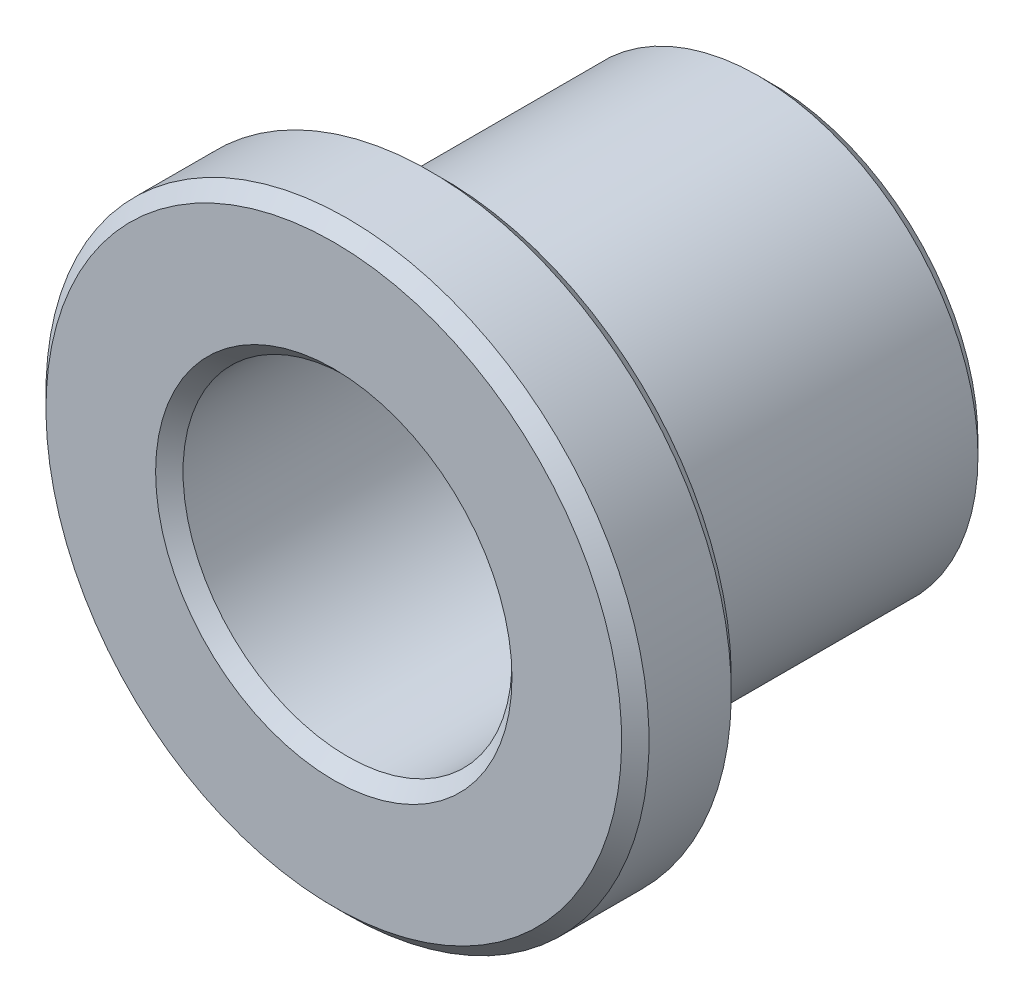
SolidWorks part; units mm, degrees
material "1.0114 (S235J0)"
ref_plane "Front Plane" through (0, 0, 0) normal (0, 0, 1) x (1, 0, 0)
ref_plane "Top Plane" through (0, 0, 0) normal (0, 1, 0) x (1, 0, 0)
ref_plane "Right Plane" through (0, 0, 0) normal (1, 0, 0) x (0, 0, -1)
sketch "Sketch1" plane through (0, 0, 0) normal (1, 0, 0) x (0, 0, -1)
  line L0 (0, 0) -> (8, 0) construction
  line L1 (0, 3) -> (0, 5.5)
  line L3 (0, 5.5) -> (2, 5.5)
  line L4 (2, 5.5) -> (2, 4)
  line L5 (2, 4) -> (8, 4)
  line L6 (8, 4) -> (8, 3)
  line L7 (8, 3) -> (0, 3)
revolve "Revolve1" add sketch "Sketch1" angle 360 about L0
chamfer "Chamfer1" distance 0.25 angle 45 5 edges at (0, -3, -8) (0, -4, -8) (0, -3, 0) (0, -5.5, -2) (0, -5.5, 0)
equation "\"D7@Sketch1\" = \"Išorinis diam.@Sketch1\" / 4"
equation "\"D5@Sketch1\" = \"Išorinis diam.@Sketch1\" * 1.375"
